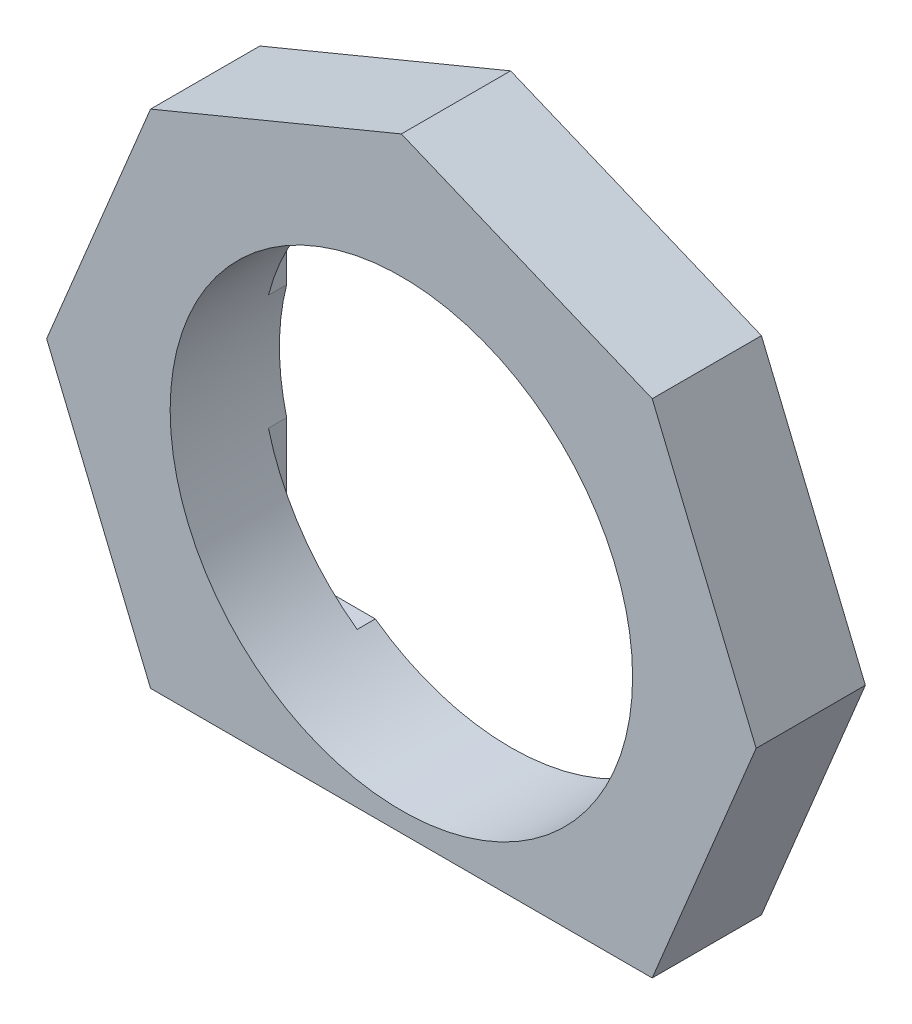
SolidWorks part; units mm, degrees
ref_plane "Front Plane" through (0, 0, 0) normal (0, 0, 1) x (1, 0, 0)
ref_plane "Top Plane" through (0, 0, 0) normal (0, 1, 0) x (1, 0, 0)
ref_plane "Right Plane" through (0, 0, 0) normal (1, 0, 0) x (0, 0, -1)
sketch "Sketch2" plane through (0, 0, 0) normal (0, 0, 1) x (1, 0, 0)
  line L1 (0, 9.7415) -> (-6.8883, 6.8883)
  line L2 (-6.8883, 6.8883) -> (-9.7415, 0)
  line L3 (-9.7415, 0) -> (-6.8883, -6.8883)
  line L4 (-6.8883, -6.8883) -> (0, -9.7415)
  line L5 (0, -9.7415) -> (6.8883, -6.8883)
  line L6 (6.8883, -6.8883) -> (9.7415, 0)
  line L7 (9.7415, 0) -> (6.8883, 6.8883)
  line L8 (6.8883, 6.8883) -> (0, 9.7415)
  circle A0 centre (0, 0) radius 9 construction
  dimension "D1" = 18
extrude "Boss-Extrude1" add sketch "Sketch2" along normal blind 3
sketch "Sketch4" plane through (0, 0, 0) normal (0, 0, -1) x (-1, 0, 0)
  line L1 (-6.15, -5.15) -> (6.15, -5.15)
  line L2 (-6.15, -5.15) -> (-6.15, 5.15)
  line L3 (-6.15, 5.15) -> (6.15, 5.15)
  line L4 (6.15, -5.15) -> (6.15, 5.15)
  line L5 (-6.15, -5.15) -> (6.15, 5.15) construction
  line L6 (-6.15, 5.15) -> (6.15, -5.15) construction
  point P0 (0, 0)
  dimension "D1" = 12.3
  dimension "D2" = 10.3
extrude "Cut-Extrude2" cut sketch "Sketch4" against normal blind 0.5
fillet "Fillet1" radius 0.5 4 edges at (6.15, -5.15, 0.25) (-6.15, -5.15, 0.25) (-6.15, 5.15, 0.25) (6.15, 5.15, 0.25)
hole_wizard "1/2-20 Tapped Hole1" positions "Sketch5" profile "Sketch6" tap size "1/2-20" standard "ANSI Inch" end condition through all
sketch "Sketch5" plane through (0, 0, 3) normal (0, 0, 1) x (1, 0, 0)
  point P0 (0, 0)
sketch "Sketch6" plane through (0, 0, 3) normal (1, 0, 0) x (0, -1, 0)
  line L0 (0, 0) -> (0, 3)
  line L1 (0, 3) -> (6.35, 3)
  line L2 (6.35, 3) -> (6.35, 0)
  line L5 (6.35, 0) -> (0, 0)
  line L11 (0, -6.35) -> (0, 107.95) construction
  dimension "Thread Major Dia." = 12.7
  dimension "Thru Tap Drill Depth" = 3
sketch "Sketch7" plane through (0, 0, 0) normal (0, 0, -1) x (-1, 0, 0)
  line L0 (-6.8883, -6.8883) -> (6.8883, -6.8883)
  line L1 (6.8883, -6.8883) -> (0, -9.7415)
  line L2 (0, -9.7415) -> (-6.8883, -6.8883)
extrude "Cut-Extrude3" cut sketch "Sketch7" against normal up to next
